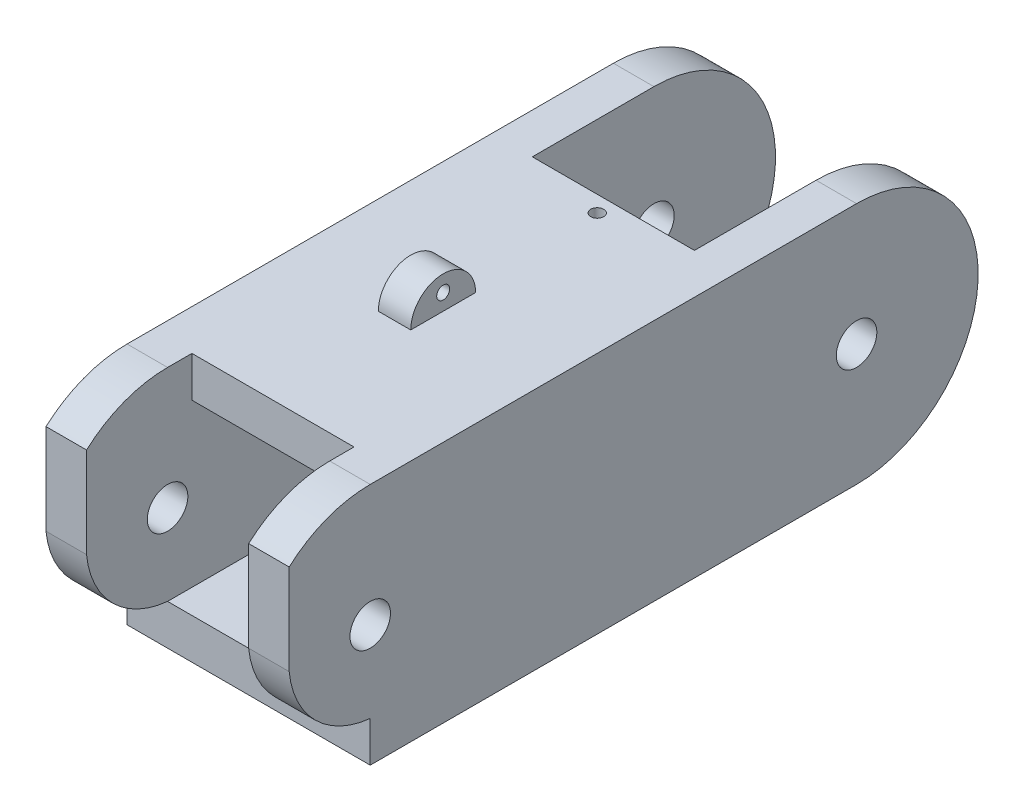
SolidWorks part; units mm, degrees
ref_plane "Front Plane" through (0, 0, 0) normal (0, 0, 1) x (1, 0, 0)
ref_plane "Top Plane" through (0, 0, 0) normal (0, 1, 0) x (1, 0, 0)
ref_plane "Right Plane" through (0, 0, 0) normal (1, 0, 0) x (0, 0, -1)
ref_plane "End Plane" through (0, 0, -31.75) normal (0, 0, 1) x (1, 0, 0)
ref_plane "Inside Plane" through (0, 19.05, 0) normal (0, 1, 0) x (1, 0, 0)
sketch "Sketch1" plane through (0, 0, 0) normal (0, 1, 0) x (1, 0, 0)
  line L1 (0, 0) -> (19.05, 0)
  line L2 (0, 0) -> (0, 57.15)
  line L3 (0, 57.15) -> (19.05, 57.15)
  line L4 (19.05, 0) -> (19.05, 57.15)
  dimension "D1" = 57.15
  dimension "D2" = 19.05
extrude "Boss-Extrude1" add sketch "Sketch1" along normal blind 19.05
sketch "Sketch2" plane through (0, 0, 0) normal (0, 0, 1) x (1, 0, 0)
  line L0 (0, 19.05) -> (19.05, 19.05) construction
  line L1 (3.175, 15.875) -> (15.875, 15.875)
  line L2 (3.175, 15.875) -> (3.175, 3.175)
  line L3 (3.175, 3.175) -> (15.875, 3.175)
  line L4 (15.875, 15.875) -> (15.875, 3.175)
  line L5 (0, 19.05) -> (0, 0) construction
  line L6 (0, 0) -> (19.05, 0) construction
  line L7 (19.05, 19.05) -> (19.05, 0) construction
  dimension "D1" = 3.175
  dimension "D2" = 3.175
  dimension "D3" = 3.175
  dimension "D4" = 3.175
extrude "Cut-Extrude1" cut sketch "Sketch2" against normal blind 76.2
sketch "Sketch3" plane through (0, 19.05, 0) normal (0, 1, 0) x (1, 0, 0)
  line L0 (0, 57.15) -> (0, 0) construction
  line L1 (7.62, 26.67) -> (10.16, 26.67)
  line L2 (7.62, 26.67) -> (7.62, 21.59)
  line L3 (7.62, 21.59) -> (10.16, 21.59)
  line L4 (10.16, 26.67) -> (10.16, 21.59)
  line L5 (0, 0) -> (19.05, 0) construction
  dimension "D1" = 2.54
  dimension "D2" = 7.62
  dimension "D3" = 21.59
  dimension "D4" = 5.08
extrude "Boss-Extrude2" add sketch "Sketch3" along normal blind 2.54
sketch "Sketch4" plane through (0, 0, 0) normal (1, 0, 0) x (0, 0, -1)
  line L0 (26.67, 19.05) -> (21.59, 19.05) construction
  line L1 (24.13, 21.59) -> (24.13, 20.32) construction
  line L2 (57.15, 19.05) -> (0, 19.05) construction
  line L3 (21.59, 21.59) -> (26.67, 21.59) construction
  line L4 (57.15, 0) -> (0, 0) construction
  line L5 (0, 19.05) -> (0, 0) construction
  circle A0 centre (24.13, 20.32) radius 0.508
  arc A1 (26.67, 19.05) -> (21.59, 19.05) centre (24.13, 21.3579) ccw
  circle A4 centre (9.525, 9.525) radius 1.5875
  arc A6 (9.525, 19.05) -> (9.525, 0) centre (9.525, 9.525) ccw
  arc A7 (9.525, 19.05) -> (9.525, 0) centre (-8.7829, 9.525) ccw
  ellipse E0 centre (24.13, 19.05) end of major axis (21.59, 19.05) minor radius 2.54 (26.67, 19.05) -> (21.59, 19.05) ccw
  dimension "D1" = 1.27
  dimension "D4" = 9.525
  dimension "D5" = 9.525
extrude "Cut-Extrude2" cut sketch "Sketch4" along normal blind 19.05
fillet "Fillet1" [suppressed] radius 0.635
fillet "Fillet2" [suppressed] radius 2.54
sketch "Sketch7" plane through (0, 19.05, 0) normal (0, 1, 0) x (1, 0, 0)
  line L2 (3.175, 0) -> (3.175, 11.43)
  line L3 (3.175, 11.43) -> (6.35, 11.43)
  line L6 (15.875, 0) -> (15.875, 11.43)
  line L7 (15.875, 11.43) -> (12.7, 11.43)
  line L10 (3.175, 0) -> (15.875, 0)
  line L11 (0, 57.15) -> (0, 9.525) construction
  line L12 (6.35, 11.43) -> (12.7, 11.43)
  line L13 (10.16, 26.67) -> (7.62, 26.67) construction
  circle A0 centre (9.525, 36.83) radius 0.508
  dimension "D5" = 9.525
  dimension "D1" = 3.175
  dimension "D2" = 3.175
  dimension "D3" = 11.43
  dimension "D4" = 11.43
  dimension "D6" = 10.16
extrude "Cut-Extrude3" cut sketch "Sketch7" against normal blind 12.7
sketch "Sketch8" plane through (0, 19.05, 0) normal (0, 1, 0) x (1, 0, 0)
  line L0 (3.175, 0) -> (3.175, 9.525) construction
  line L1 (3.175, 0) -> (15.875, 0)
  line L2 (3.175, 0) -> (3.175, 9.525)
  line L3 (3.175, 9.525) -> (15.875, 9.525)
  line L4 (15.875, 0) -> (15.875, 9.525)
extrude "Cut-Extrude4" cut sketch "Sketch8" against normal blind 25.4
sketch "Sketch9" plane through (0, 0, 0) normal (0, 1, 0) x (1, 0, 0)
  line L0 (3.175, 9.525) -> (15.875, 9.525) construction
  line L1 (12.065, 22.225) -> (8.255, 22.225)
  line L2 (12.065, 22.225) -> (12.065, 27.305)
  line L3 (12.065, 27.305) -> (8.255, 27.305)
  line L4 (8.255, 22.225) -> (8.255, 27.305)
  line L5 (19.05, 9.525) -> (19.05, 57.15) construction
  dimension "D1" = 3.81
  dimension "D2" = 5.08
  dimension "D3" = 12.7
  dimension "D4" = 6.985
extrude "Boss-Extrude3" [suppressed] add sketch "Sketch9" against normal blind 5.08
sketch "Sketch10" [suppressed] plane through (0, 0, 0) normal (1, 0, 0) x (0, 0, -1)
  line L0 (27.305, -5.08) -> (27.305, 0) construction
  line L1 (22.225, -5.08) -> (27.305, -5.08) construction
  line L2 (22.225, -5.08) -> (22.225, 0) construction
  line L3 (22.225, 0) -> (27.305, 0) construction
  line L4 (22.225, -2.54) -> (22.225, 0)
  line L5 (25.1652, 0) -> (27.305, 0)
  line L6 (9.525, 0) -> (41.275, 0) construction
  arc A0 (27.305, -2.54) -> (24.765, -5.08) centre (24.765, -2.54) cw
  arc A1 (24.765, -5.08) -> (22.225, -2.54) centre (24.765, -2.54) cw
  arc A2 (27.305, -2.54) -> (26.0285, -1.3339) centre (26.0637, -2.5752) ccw
  arc A3 (26.0285, -1.3339) -> (26.0483, -2.0347) centre (26.0384, -1.6843) ccw
  arc A4 (26.0483, -2.0347) -> (26.68, -2.5752) centre (26.0422, -2.6811) cw
  arc A5 (26.68, -2.5752) -> (24.765, -4.4612) centre (24.5539, -2.3316) cw
  arc A6 (24.765, -4.4612) -> (22.9012, -2.54) centre (25.0593, -2.311) cw
  arc A7 (22.9012, -2.54) -> (25.1652, 0) centre (27.0171, -3.9296) cw
  arc A8 (27.305, 0) -> (22.225, 0) centre (24.765, -2.8187) cw
extrude "Cut-Extrude5" [suppressed] cut sketch "Sketch10" along normal blind 25.4
sketch "Sketch11" plane through (0, 0, 0) normal (1, 0, 0) x (0, 0, -1)
  line L3 (9.525, 19.05) -> (57.15, 19.05) construction
  line L4 (9.525, 0) -> (57.15, 0) construction
  line L5 (57.15, 19.05) -> (57.15, 0) construction
  circle A0 centre (47.625, 9.525) radius 1.5875
  arc A1 (47.625, 0) -> (47.625, 19.05) centre (47.625, 9.525) ccw
  arc A2 (47.625, 19.05) -> (47.625, 0) centre (52.9788, 9.525) cw
extrude "Cut-Extrude6" cut sketch "Sketch11" along normal blind 19.05
sketch "Sketch12" plane through (0, 19.05, 0) normal (0, 1, 0) x (1, 0, 0)
  line L0 (19.05, 47.625) -> (0, 47.625) construction
  line L1 (3.175, 69.071) -> (15.875, 69.071)
  line L2 (3.175, 69.071) -> (3.175, 38.1)
  line L3 (3.175, 38.1) -> (15.875, 38.1)
  line L4 (15.875, 69.071) -> (15.875, 38.1)
  dimension "D1" = 9.525
extrude "Cut-Extrude7" cut sketch "Sketch12" against normal blind 3.81
sketch "Sketch13" plane through (0, 0, 0) normal (0, 1, 0) x (1, 0, 0)
  line L1 (3.175, 67.0881) -> (15.875, 67.0881)
  line L2 (3.175, 67.0881) -> (3.175, 47.625)
  line L3 (3.175, 47.625) -> (15.875, 47.625)
  line L4 (15.875, 67.0881) -> (15.875, 47.625)
extrude "Cut-Extrude8" cut sketch "Sketch13" along normal blind 3.81
sketch "Sketch14" plane through (0, 0, 0) normal (1, 0, 0) x (0, 0, -1)
  line L0 (9.525, 0) -> (9.525, 3.175)
  line L1 (3.175, 9.525) -> (3.175, 18.7413)
  line L3 (3.175, 18.7413) -> (-3.7286, 9.9787)
  line L4 (-3.7286, 9.9787) -> (-2.5445, 0)
  line L5 (-2.5445, 0) -> (9.525, 0)
  arc A1 (3.175, 9.525) -> (9.525, 3.175) centre (10.2236, 10.2236) ccw
  arc A3 (9.525, 19.05) -> (9.525, 0) centre (9.525, 9.525) ccw construction
  point P7 (0, 9.525)
  dimension "D2" = 3.175
  dimension "D1" = 3.175
extrude "Cut-Extrude9" cut sketch "Sketch14" along normal blind 19.05
